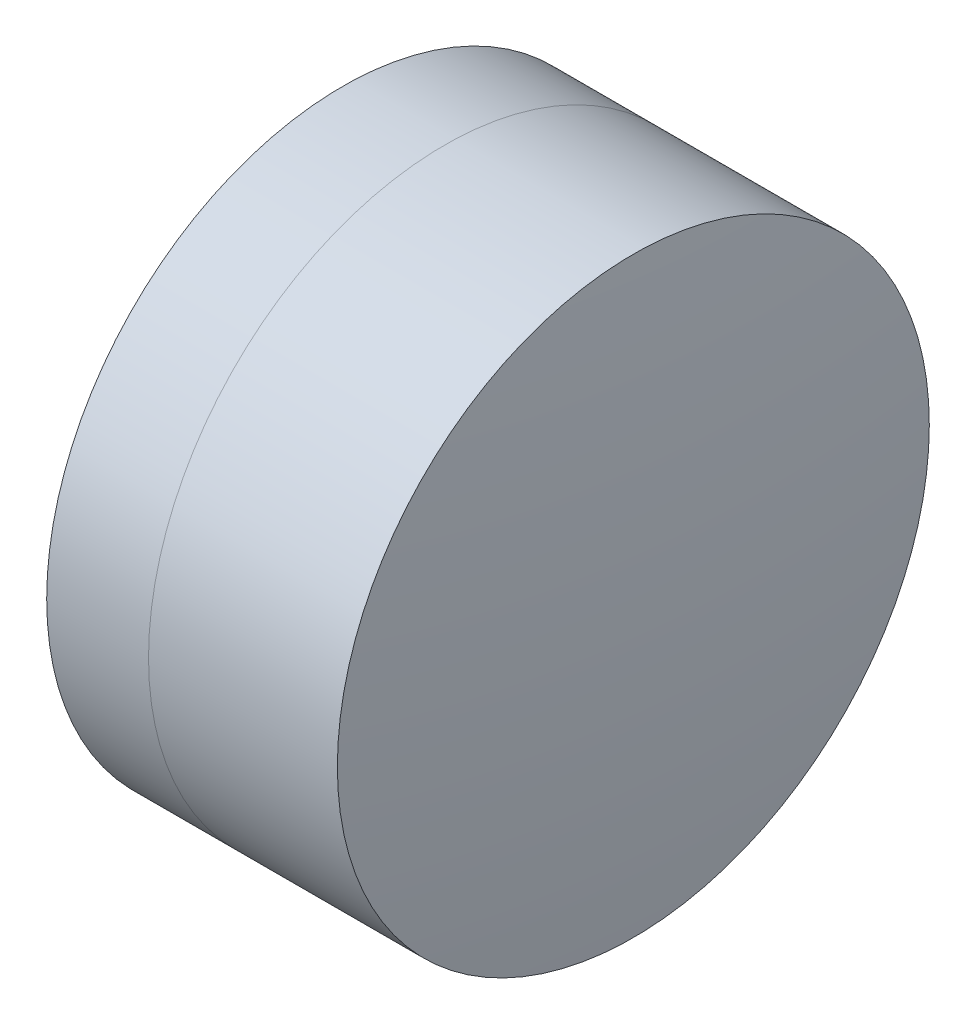
SolidWorks part; units mm, degrees
ref_plane "前视基准面" through (0, 0, 0) normal (0, 0, 1) x (1, 0, 0)
ref_plane "上视基准面" through (0, 0, 0) normal (0, 1, 0) x (1, 0, 0)
ref_plane "右视基准面" through (0, 0, 0) normal (1, 0, 0) x (0, 0, -1)
sketch "草图1" plane through (0, 0, 0) normal (0, 1, 0) x (1, 0, 0)
  line L0 (124.5233, 0) -> (646.9917, 0) construction
  line L1 (260.5883, -3.175) -> (261.6807, -3.175)
  line L2 (260.5883, 3.175) -> (261.6807, 3.175)
  arc A0 (261.6807, -3.175) -> (261.6807, 3.175) centre (255.7807, 0) ccw
  arc A1 (260.5883, 3.175) -> (260.5883, -3.175) centre (268.5807, 0) ccw
  point P10 (259.9807, 0)
  point P11 (262.4807, 0)
  dimension "D3" = 8.6
  dimension "D4" = 6.7
  dimension "D1" = 3.175
  dimension "D2" = 3.175
  dimension "D5" = 2.5
revolve "旋转1" add sketch "草图1" angle 360 about L0
sketch "草图2" plane through (0, 0, 0) normal (0, 1, 0) x (1, 0, 0)
  line L0 (-0.5519, 0) -> (622.6607, 0) construction
  line L2 (261.6807, 3.175) -> (263.7064, 3.175)
  line L3 (261.6807, -3.175) -> (263.7064, -3.175)
  arc A0 (263.7064, -3.175) -> (263.7064, 3.175) centre (234.8807, 0) ccw
  arc A1 (261.6807, -3.175) -> (261.6807, 3.175) centre (255.7807, 0) ccw construction
  arc A2 (261.6807, -3.175) -> (261.6807, 3.175) centre (255.7807, 0) ccw
  point P4 (262.4807, 0)
  point P8 (263.8807, 0)
  dimension "D1" = 29
  dimension "D2" = 1.4
revolve "旋转3" add sketch "草图2" angle 360 about L0
